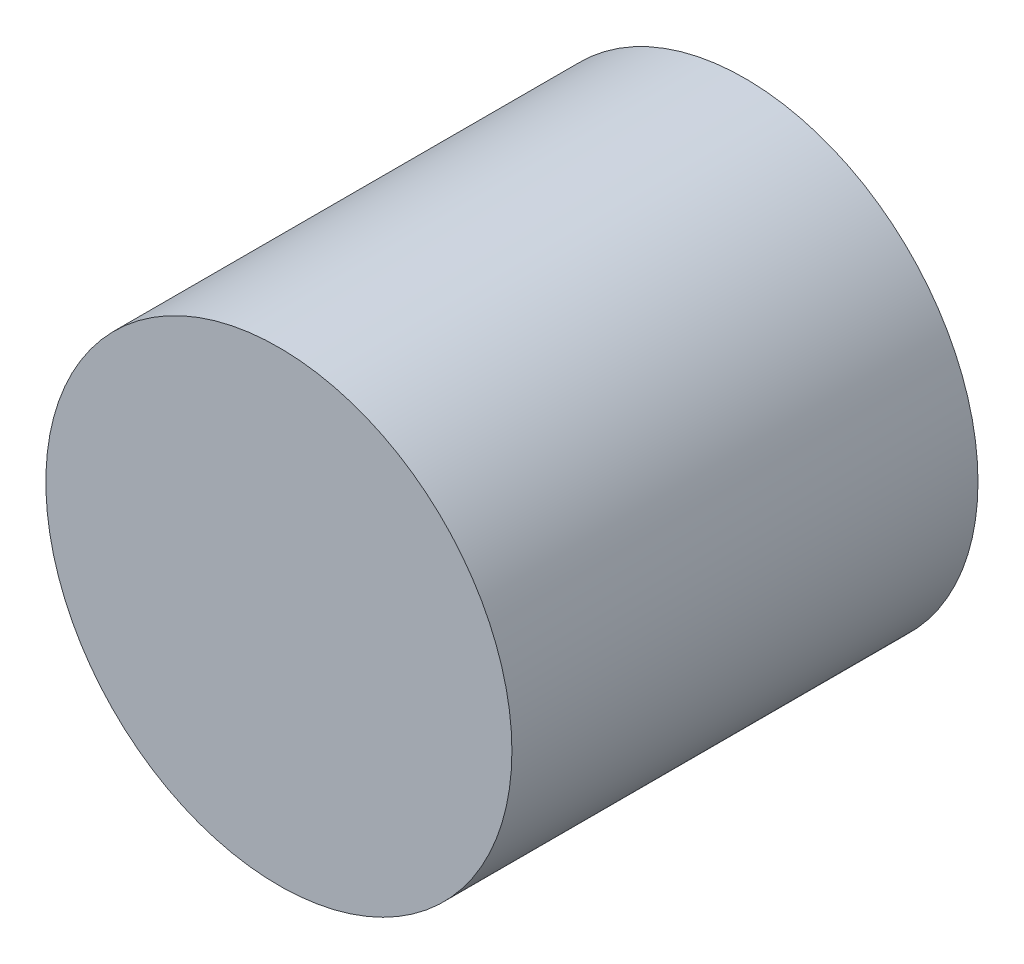
SolidWorks part; units mm, degrees
ref_plane "Front Plane" through (0, 0, 0) normal (0, 0, 1) x (1, 0, 0)
ref_plane "Top Plane" through (0, 0, 0) normal (0, 1, 0) x (1, 0, 0)
ref_plane "Right Plane" through (0, 0, 0) normal (1, 0, 0) x (0, 0, -1)
sketch "Sketch1" plane through (0, 0, 0) normal (0, 0, 1) x (1, 0, 0)
  circle A0 centre (0, 0) radius 12.7
  dimension "D1" = 25.4
extrude "Boss-Extrude1" add sketch "Sketch1" along normal blind 25.4
